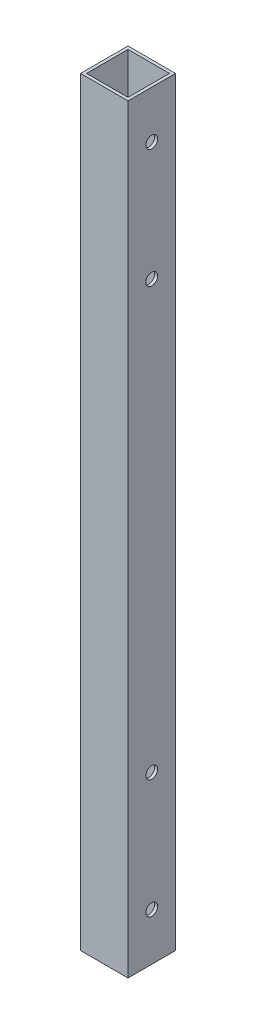
SolidWorks part; units mm, degrees
material "6061 Alloy"
ref_plane "Front Plane" through (0, 0, 0) normal (0, 0, 1) x (1, 0, 0)
ref_plane "Top Plane" through (0, 0, 0) normal (0, 1, 0) x (1, 0, 0)
ref_plane "Right Plane" through (0, 0, 0) normal (1, 0, 0) x (0, 0, -1)
sketch "Sketch1" plane through (0, 0, 0) normal (0, 1, 0) x (1, 0, 0)
  line L0 (-25.4, -25.4) -> (25.4, 25.4) construction
  line L1 (-25.4, 25.4) -> (25.4, 25.4)
  line L2 (-25.4, 25.4) -> (-25.4, -25.4)
  line L3 (-25.4, -25.4) -> (25.4, -25.4)
  line L4 (25.4, 25.4) -> (25.4, -25.4)
  line L5 (22.225, -22.225) -> (-22.225, 22.225) construction
  line L6 (-22.225, 22.225) -> (22.1918, 22.225)
  line L7 (-22.225, 22.225) -> (-22.225, -22.1918)
  line L8 (-22.225, -22.1918) -> (22.1918, -22.1918)
  line L9 (22.1918, 22.225) -> (22.1918, -22.1918)
  point P7 (0, 0)
  point P10 (0, 0)
  point P11 (0, 0)
  point P14 (0, 0)
  dimension "D1" = 50.8
  dimension "D2" = 3.175
  dimension "D3" = 3.175
extrude "Boss-Extrude1" add sketch "Sketch1" along normal blind 812.8
sketch "Sketch2" plane through (-25.4, 0, 0) normal (-1, 0, 0) x (0, 0, 1)
  line L0 (25.4, 406.4) -> (-25.4, 406.4) construction
  line L1 (25.4, 812.8) -> (25.4, 0) construction
  line L2 (-25.4, 812.8) -> (-25.4, 0) construction
  line L3 (0, 50.8) -> (0, 762) construction
  line L4 (0, 635) -> (0, 177.8) construction
  circle A0 centre (0, 50.8) radius 6.35
  circle A1 centre (0, 177.8) radius 6.35
  circle A2 centre (0, 635) radius 6.35
  circle A3 centre (0, 762) radius 6.35
  point P10 (0, 406.4)
  point P13 (0, 406.4)
  dimension "D3" = 12.7
extrude "Cut-Extrude1" cut sketch "Sketch2" against normal through all
equation "\"D1@Boss-Extrude1\"=\"HoleDist\"+4"
